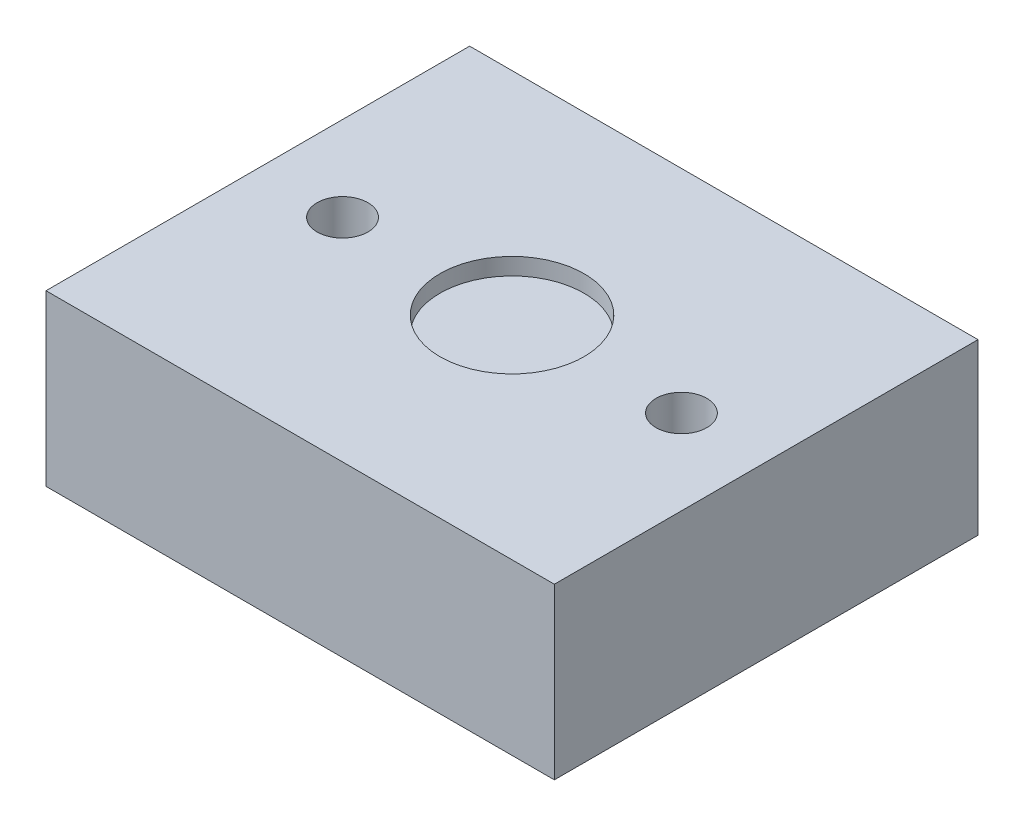
SolidWorks part; units mm, degrees
ref_plane "Front Plane" through (0, 0, 0) normal (0, 0, 1) x (1, 0, 0)
ref_plane "Top Plane" through (0, 0, 0) normal (0, 1, 0) x (1, 0, 0)
ref_plane "Right Plane" through (0, 0, 0) normal (1, 0, 0) x (0, 0, -1)
sketch "Sketch1" plane through (0, 0, 0) normal (0, 1, 0) x (1, 0, 0)
  line L0 (-10, 0) -> (-15, 0) construction
  line L1 (-15, -12.5) -> (15, -12.5)
  line L2 (-15, -12.5) -> (-15, 12.5)
  line L3 (-15, 12.5) -> (15, 12.5)
  line L4 (15, -12.5) -> (15, 12.5)
  line L5 (-15, -12.5) -> (15, 12.5) construction
  line L6 (-15, 12.5) -> (15, -12.5) construction
  line L7 (10, 0) -> (15, 0) construction
  circle A0 centre (10, 0) radius 1.5
  circle A1 centre (-10, 0) radius 1.5
  point P0 (0, 0)
  dimension "D2" = 3
  dimension "D3" = 3
  dimension "D1" = 30
  dimension "25" = 25
  dimension "D4" = 20
extrude "Boss-Extrude1" add sketch "Sketch1" along normal blind 10
sketch "Sketch3" plane through (0, 10, 0) normal (0, 1, 0) x (1, 0, 0)
  circle A0 centre (0, 0) radius 4.25
  dimension "D1" = 8.5
extrude "Cut-Extrude1" cut sketch "Sketch3" against normal blind 1
